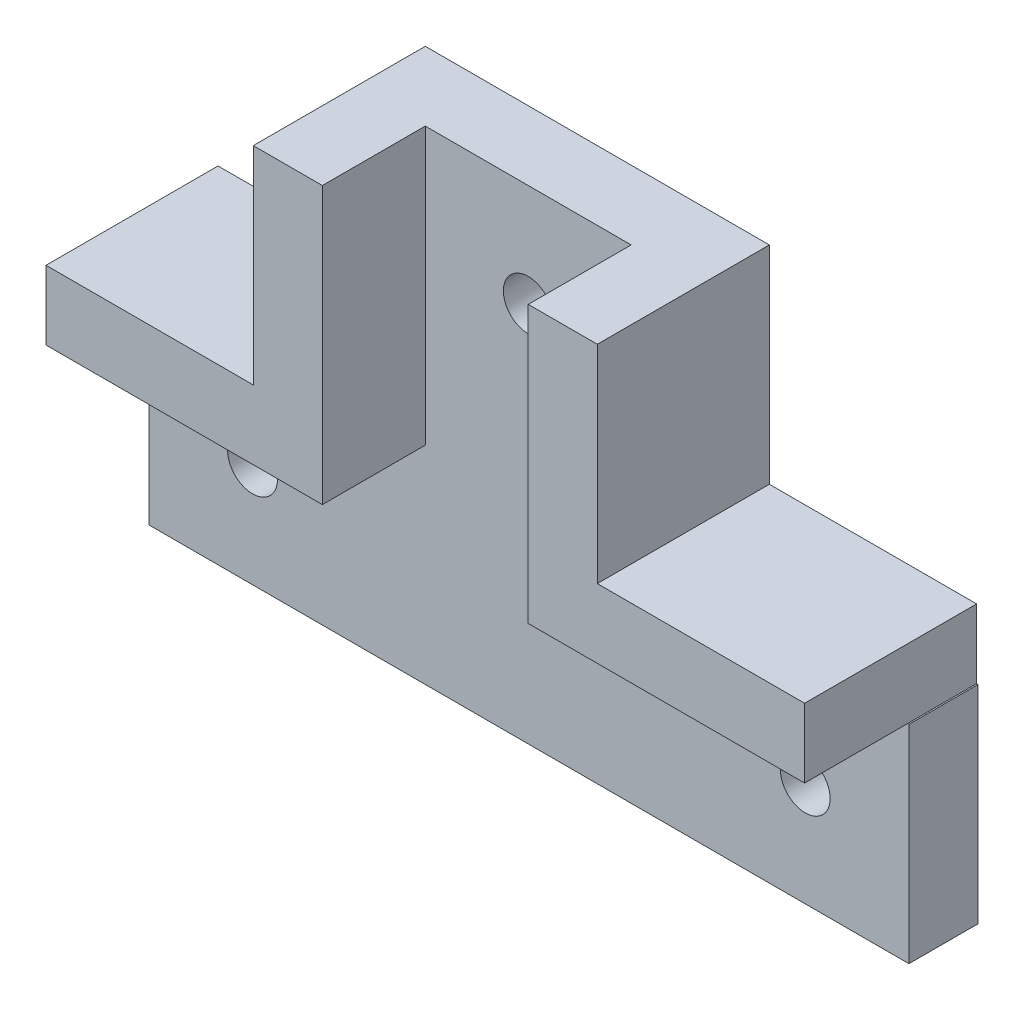
SolidWorks part; units mm, degrees
ref_plane "Front Plane" through (0, 0, 0) normal (0, 0, 1) x (1, 0, 0)
ref_plane "Top Plane" through (0, 0, 0) normal (0, 1, 0) x (1, 0, 0)
ref_plane "Right Plane" through (0, 0, 0) normal (1, 0, 0) x (0, 0, -1)
sketch "Sketch1" plane through (0, 0, 0) normal (0, 0, 1) x (1, 0, 0)
  line L0 (14.3137, -4.2647) -> (34.3137, -4.2647)
  line L1 (-20.6863, -4.2647) -> (-0.6863, -4.2647)
  line L2 (-20.6863, -4.2647) -> (-20.6863, -19.2647)
  line L3 (-20.6863, -19.2647) -> (34.3137, -19.2647)
  line L4 (34.3137, -4.2647) -> (34.3137, -19.2647)
  line L5 (-0.6863, 15.7353) -> (14.3137, 15.7353)
  line L6 (-0.6863, 15.7353) -> (-0.6863, -4.2647)
  line L8 (14.3137, 15.7353) -> (14.3137, -4.2647)
  dimension "D1" = 15
  dimension "D2" = 20
  dimension "D3" = 20
  dimension "D4" = 15
  dimension "D5" = 20
extrude "Boss-Extrude1" add sketch "Sketch1" along normal blind 5
sketch "Sketch2" plane through (0, 0, 0) normal (0, 0, -1) x (-1, 0, 0)
  line L0 (0.6863, 15.7353) -> (5.6863, 15.7353)
  line L1 (5.6863, 15.7353) -> (5.6863, 0.7353)
  line L2 (20.6863, -4.2647) -> (20.6863, 0.7353)
  line L3 (20.6863, 0.7353) -> (6.08, 0.7353)
  line L4 (20.6863, -4.2647) -> (0.6863, -4.2647)
  line L5 (0.6863, 15.7353) -> (0.6863, -4.2647)
  line L6 (6.08, 0.7353) -> (5.6863, 0.7353)
  dimension "D1" = 5
  dimension "D2" = 5
extrude "Boss-Extrude2" add sketch "Sketch2" against normal blind 12.45 contours L3 L6 L1 L0 L5 L4 L2
sketch "Sketch4" plane through (0, 0, 0) normal (0, 0, -1) x (-1, 0, 0)
  line L0 (20.6863, -19.2647) -> (-34.3137, -19.2647)
  line L1 (-34.3137, -19.2647) -> (-34.3137, -24.2647)
  line L2 (-34.3137, -24.2647) -> (20.6863, -24.2647)
  line L3 (20.6863, -24.2647) -> (20.6863, -19.2647)
  dimension "D1" = 5
ref_plane "Plane4" through (6.7637, 0, 0) normal (-1, 0, 0) x (0, 0, 1)
ref_plane "Plane5" through (-5.7363, 0, 0) normal (-1, 0, 0) x (0, 0, 1)
mirror "Mirror1" about plane through (6.7637, 0, 0) normal (-1, 0, 0) of "Boss-Extrude2"
sketch "Sketch6" plane through (0, 0, 5) normal (0, 0, 1) x (1, 0, 0)
  line L0 (6.7637, 6.8475) -> (6.7637, -6.8475) construction
  line L1 (-20.6863, -4.2647) -> (-20.6863, -19.2647) construction
  line L2 (-20.6863, -4.2647) -> (-0.6863, -4.2647) construction
  line L3 (34.2137, -4.2647) -> (14.2137, -4.2647) construction
  line L5 (34.3137, -19.2647) -> (34.3137, -4.2647) construction
  line L6 (14.2137, 15.7353) -> (-0.6863, 15.7353) construction
  circle A0 centre (6.7637, 8.2353) radius 1.8
  circle A1 centre (-13.1863, -11.7647) radius 1.8
  circle A2 centre (26.8137, -11.7647) radius 1.8
  dimension "D1" = 3.6
  dimension "D2" = 3.6
  dimension "D3" = 3.6
  dimension "D5" = 7.5
  dimension "D7" = 7.5
  dimension "D8" = 7.5
  dimension "D4" = 7.5
  dimension "D6" = 7.5
ref_plane "Plane6" through (-5.6863, 0.7353, 12.45) normal (0, -1, 0) x (-1, 0, 0)
extrude "Cut-Extrude3" cut sketch "Sketch6" against normal through all
